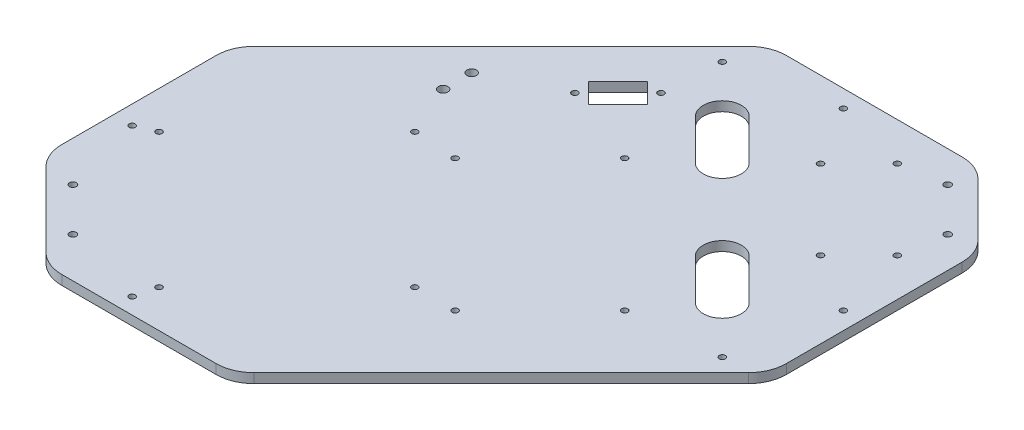
SolidWorks part; units mm, degrees
ref_plane "Front Plane" through (0, 0, 0) normal (0, 0, 1) x (1, 0, 0)
ref_plane "Top Plane" through (0, 0, 0) normal (0, 1, 0) x (1, 0, 0)
ref_plane "Right Plane" through (0, 0, 0) normal (1, 0, 0) x (0, 0, -1)
sketch "Sketch1" plane through (0, 0, 0) normal (0, 1, 0) x (1, 0, 0)
  line L0 (-40.2018, 94.8407) -> (89.59, 224.6325)
  line L1 (-51.0597, 235.4904) -> (248.9403, 235.4904) construction
  line L2 (-51.0597, 235.4904) -> (-51.0597, -64.5096) construction
  line L3 (-51.0597, -64.5096) -> (248.9403, -64.5096) construction
  line L4 (248.9403, 235.4904) -> (248.9403, -64.5096) construction
  line L5 (210.3007, 224.6325) -> (238.0824, 196.8508)
  line L6 (-40.2018, -14.5563) -> (-1.1064, -53.6517)
  line L7 (238.0824, 76.1401) -> (108.2906, -53.6517)
  line L8 (248.9403, 235.4904) -> (-51.0597, -64.5096) construction
  line L9 (-24.8968, -15.7192) -> (-2.2693, -38.3466) construction
  line L10 (204.9129, 214.0905) -> (227.5404, 191.4631) construction
  line L11 (-46.0597, 80.6986) -> (-46.0597, -0.4141)
  line L12 (13.0357, -59.5096) -> (94.1484, -59.5096)
  line L13 (243.9403, 90.2823) -> (243.9403, 182.7087)
  line L14 (103.7321, 230.4904) -> (196.1585, 230.4904)
  line L15 (-36.1976, 26.6943) -> (41.5841, -51.0874) construction
  line L16 (40.8642, 98.125) -> (111.5748, 27.4143) construction
  line L17 (40.8642, 98.125) -> (-26.311, 30.9498) construction
  line L18 (-26.311, 30.9498) -> (44.3997, -39.7609) construction
  line L19 (111.5748, 27.4143) -> (44.3997, -39.7609) construction
  line L20 (108.0393, 141.2585) -> (177.3358, 71.962) construction
  line L21 (108.0393, 141.2585) -> (63.4916, 96.7108) construction
  line L22 (63.4916, 96.7108) -> (132.788, 27.4143) construction
  line L23 (177.3358, 71.962) -> (132.788, 27.4143) construction
  line L24 (182.1187, 210.3881) -> (223.838, 168.6688) construction
  line L25 (182.1187, 210.3881) -> (161.9662, 190.2356) construction
  line L26 (161.9662, 190.2356) -> (203.6855, 148.5163) construction
  line L27 (223.838, 168.6688) -> (203.6855, 148.5163) construction
  line L28 (114.59, 185.9929) -> (135.8032, 164.7797) construction
  line L29 (121.6611, 193.064) -> (142.8743, 171.8508)
  line L30 (107.5189, 178.9219) -> (128.7321, 157.7087)
  line L31 (178.2296, 122.3533) -> (199.4428, 101.1401) construction
  line L32 (185.3007, 129.4244) -> (206.5139, 108.2112)
  line L33 (171.1585, 115.2823) -> (192.3717, 94.0691)
  line L34 (89.8413, 210.7417) -> (224.1915, 76.3914) construction
  line L35 (65.2469, 157.863) -> (87.8743, 180.4904) construction
  line L36 (142.8743, 221.3483) -> (234.7982, 129.4244) construction
  line L37 (28.9403, 139.9412) -> (28.9403, 124.9412) construction
  line L38 (71.2573, 174.48) -> (81.8639, 163.8734) construction
  line L39 (63.4791, 166.7018) -> (74.0857, 156.0952)
  line L40 (63.4791, 166.7018) -> (79.0354, 182.2582)
  line L41 (79.0354, 182.2582) -> (89.642, 171.6516)
  line L42 (89.642, 171.6516) -> (74.0857, 156.0952)
  circle A0 centre (-24.8968, -15.7192) radius 1.8
  circle A1 centre (-2.2693, -38.3466) radius 1.8
  circle A2 centre (204.9129, 214.0905) radius 1.8
  circle A3 centre (227.5404, 191.4631) radius 1.8
  arc A4 (-46.0597, 80.6986) -> (-40.2018, 94.8407) centre (-26.0597, 80.6986) cw
  arc A5 (-46.0597, -0.4141) -> (-40.2018, -14.5563) centre (-26.0597, -0.4141) ccw
  arc A6 (13.0357, -59.5096) -> (-1.1064, -53.6517) centre (13.0357, -39.5096) cw
  arc A7 (94.1484, -59.5096) -> (108.2906, -53.6517) centre (94.1484, -39.5096) ccw
  arc A8 (243.9403, 90.2823) -> (238.0824, 76.1401) centre (223.9403, 90.2823) cw
  arc A9 (243.9403, 182.7087) -> (238.0824, 196.8508) centre (223.9403, 182.7087) ccw
  arc A10 (196.1585, 230.4904) -> (210.3007, 224.6325) centre (196.1585, 210.4904) cw
  arc A11 (103.7321, 230.4904) -> (89.59, 224.6325) centre (103.7321, 210.4904) ccw
  circle A12 centre (-26.311, 30.9498) radius 1.6
  circle A13 centre (44.3997, -39.7609) radius 1.6
  circle A14 centre (111.5748, 27.4143) radius 1.6
  circle A15 centre (40.8642, 98.125) radius 1.6
  circle A16 centre (-36.1976, 26.6943) radius 1.6
  circle A17 centre (41.5841, -51.0874) radius 1.6
  circle A18 centre (63.4916, 96.7108) radius 1.6
  circle A19 centre (132.788, 27.4143) radius 1.6
  circle A20 centre (177.3358, 71.962) radius 1.6
  circle A21 centre (108.0393, 141.2585) radius 1.6
  circle A22 centre (161.9662, 190.2356) radius 1.6
  circle A23 centre (203.6855, 148.5163) radius 1.6
  circle A24 centre (223.838, 168.6688) radius 1.6
  circle A25 centre (182.1187, 210.3881) radius 1.6
  arc A26 (121.6611, 193.064) -> (107.5189, 178.9219) centre (114.59, 185.9929) ccw
  arc A27 (128.7321, 157.7087) -> (142.8743, 171.8508) centre (135.8032, 164.7797) ccw
  arc A28 (185.3007, 129.4244) -> (171.1585, 115.2823) centre (178.2296, 122.3533) ccw
  arc A29 (192.3717, 94.0691) -> (206.5139, 108.2112) centre (199.4428, 101.1401) ccw
  circle A30 centre (89.8413, 210.7417) radius 1.6
  circle A31 centre (224.1915, 76.3914) radius 1.6
  circle A32 centre (65.2469, 157.863) radius 1.6
  circle A33 centre (87.8743, 180.4904) radius 1.6
  circle A34 centre (142.8743, 221.3483) radius 1.6
  circle A35 centre (234.7982, 129.4244) radius 1.6
  circle A36 centre (28.9403, 139.9412) radius 2.5
  circle A37 centre (28.9403, 124.9412) radius 2.5
  point P6 (76.2195, 62.7696)
  point P8 (-13.5831, -27.0329)
  point P10 (216.2266, 202.7768)
  point P61 (182.8258, 169.3759)
  point P71 (125.1966, 175.3863)
  point P76 (188.8362, 111.7467)
  point P86 (157.0164, 143.5665)
  point P95 (188.8362, 175.3863)
  point P102 (76.5606, 169.1767)
  point P103 (76.5606, 169.1767)
  point P106 (68.7824, 161.3985)
  point P109 (71.2573, 174.48)
  point P110 (0, 0)
  dimension "D6" = 3.6
  dimension "D15" = 20
  dimension "D16" = 20
  dimension "D17" = 20
  dimension "D18" = 20
  dimension "D19" = 20
  dimension "D20" = 20
  dimension "D21" = 20
  dimension "D22" = 20
  dimension "D25" = 3.2
  dimension "D27" = 110
  dimension "D28" = 3.2
  dimension "D45" = 3.2
  dimension "D50" = 15
  dimension "D51" = 5
  dimension "D1" = 300
  dimension "D2" = 300
  dimension "D3" = 210
  dimension "D4" = 32
  dimension "D5" = 32
  dimension "D7" = 325
  dimension "D8" = 43
  dimension "D9" = 35
  dimension "D10" = 10
  dimension "D11" = 5
  dimension "D12" = 5
  dimension "D13" = 5
  dimension "D14" = 5
  dimension "D23" = 95
  dimension "D24" = 100
  dimension "D26" = 85
  dimension "D29" = 75
  dimension "D30" = 98
  dimension "D31" = 63
  dimension "D32" = 195
  dimension "D33" = 65
  dimension "D34" = 28.5
  dimension "D35" = 59
  dimension "D36" = 65
  dimension "D37" = 30
  dimension "D38" = 30
  dimension "D39" = 20
  dimension "D40" = 130
  dimension "D41" = 30
  dimension "D42" = 190
  dimension "D43" = 130
  dimension "D44" = 32
  dimension "D46" = 30
  dimension "D47" = 55
  dimension "D48" = 130
  dimension "D49" = 85
  dimension "D52" = 75
  dimension "D53" = 17
  dimension "D54" = 15
  dimension "D55" = 22
extrude "Boss-Extrude1" add sketch "Sketch1" along normal blind 5
